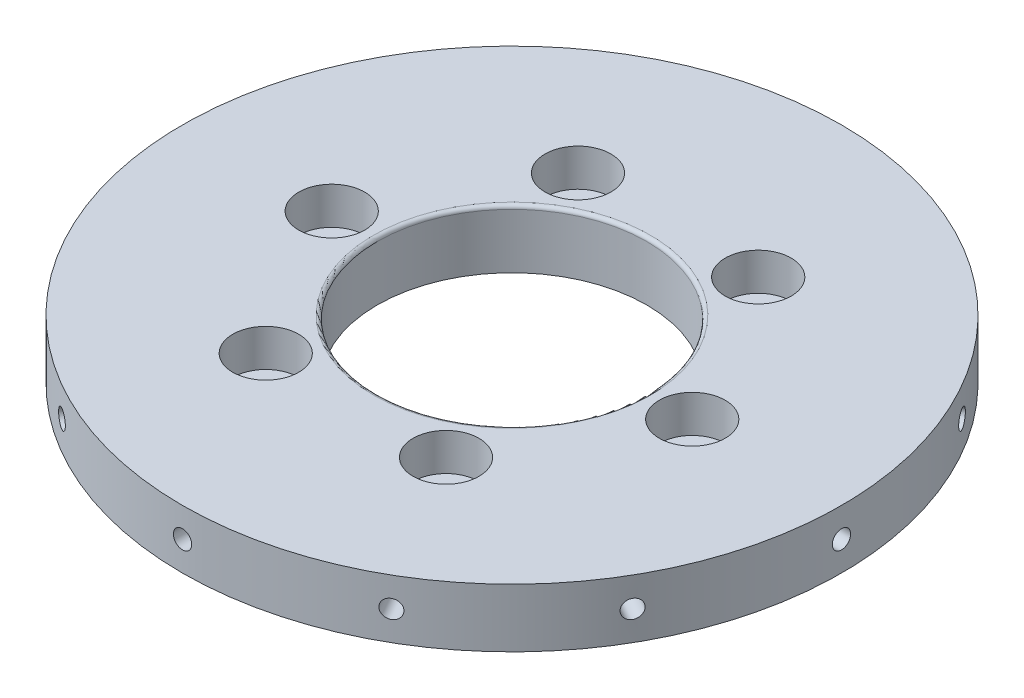
SolidWorks part; units mm, degrees
material "6061 合金"
ref_plane "前视基准面" through (0, 0, 0) normal (0, 0, 1) x (1, 0, 0)
ref_plane "上视基准面" through (0, 0, 0) normal (0, 1, 0) x (1, 0, 0)
ref_plane "右视基准面" through (0, 0, 0) normal (1, 0, 0) x (0, 0, -1)
sketch "草图1" plane through (0, 0, 0) normal (0, 1, 0) x (1, 0, 0)
  circle A0 centre (0, 0) radius 44.975
  circle A1 centre (0, 0) radius 24.6 construction
  circle A2 centre (-24.6, 0) radius 2.1
  circle A3 centre (-12.3, 21.3042) radius 2.1
  circle A4 centre (12.3, 21.3042) radius 2.1
  circle A5 centre (24.6, 0) radius 2.1
  circle A6 centre (12.3, -21.3042) radius 2.1
  circle A7 centre (-12.3, -21.3042) radius 2.1
  circle A8 centre (0, 0) radius 18.4
  point P19 (0, 0)
  dimension "D1" = 6
  dimension "D2" = 89.95
extrude "凸台-拉伸1" add sketch "草图1" along normal blind 8
sketch "草图2" plane through (0, 0, 0) normal (0, -1, 0) x (1, 0, 0)
  circle A0 centre (0, 0) radius 24.6 construction
  circle A1 centre (-21.3042, -12.3) radius 4
  circle A2 centre (0, 24.6) radius 4
  circle A3 centre (21.3042, -12.3) radius 4
  point P17 (0, 0)
  dimension "D1" = 3
extrude "切除-拉伸1" cut sketch "草图2" against normal blind 3
sketch "草图4" plane through (0, 8, 0) normal (0, 1, 0) x (1, 0, 0)
  circle A0 centre (-24.6, 0) radius 4.5
  circle A1 centre (0, 0) radius 24.6 construction
  circle A2 centre (-12.3, 21.3042) radius 4.5
  circle A3 centre (12.3, 21.3042) radius 4.5
  circle A4 centre (24.6, 0) radius 4.5
  circle A5 centre (12.3, -21.3042) radius 4.5
  circle A6 centre (-12.3, -21.3042) radius 4.5
  point P16 (0, 0)
  dimension "D1" = 6
extrude "切除-拉伸2" cut sketch "草图4" against normal blind 5.1
ref_plane "基准面1" through (45, 0, 0) normal (1, 0, 0) x (0, 0, -1)
sketch "草图5" plane through (45, 0, 0) normal (1, 0, 0) x (0, 0, -1)
  circle A0 centre (0, 4) radius 1.25
extrude "切除-拉伸3" cut sketch "草图5" against normal blind 10
pattern_circular "阵列(圆周)1" count 12 over 360 about axis through (0, 0, 0) along (0, 1, 0) of "切除-拉伸3"
fillet "圆角1" radius 0.5 1 edges at (0, 8, 18.4)
